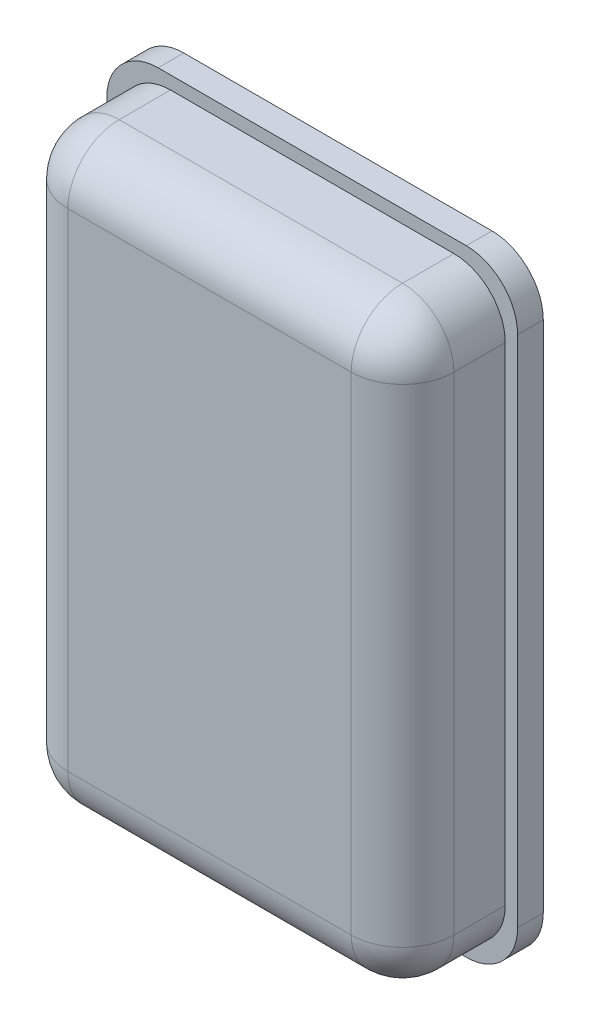
SolidWorks part; units mm, degrees
ref_plane "Alzado" through (0, 0, 0) normal (0, 0, 1) x (1, 0, 0)
ref_plane "Planta" through (0, 0, 0) normal (0, 1, 0) x (1, 0, 0)
ref_plane "Vista lateral" through (0, 0, 0) normal (1, 0, 0) x (0, 0, -1)
sketch "Croquis1" plane through (0, 0, 0) normal (0, 0, 1) x (1, 0, 0)
  line L1 (40, 60) -> (-40, 60)
  line L2 (40, 60) -> (40, -60)
  line L3 (40, -60) -> (-40, -60)
  line L4 (-40, 60) -> (-40, -60)
  line L5 (40, 60) -> (-40, -60) construction
  line L6 (40, -60) -> (-40, 60) construction
  point P0 (0, 0)
  dimension "D1" = 80
  dimension "D2" = 120
extrude "Saliente-Extruir1" add sketch "Croquis1" along normal blind 5
fillet "Redondeo2" radius 10 4 edges at (-40, -60, 2.5) (40, -60, 2.5) (-40, 60, 2.5) (40, 60, 2.5)
sketch "Croquis2" plane through (0, 0, 5) normal (0, 0, 1) x (1, 0, 0)
  line L1 (-37.5888, 57.4644) -> (37.5888, 57.4644)
  line L2 (-37.5888, 57.4644) -> (-37.5888, -57.4644)
  line L3 (-37.5888, -57.4644) -> (37.5888, -57.4644)
  line L4 (37.5888, 57.4644) -> (37.5888, -57.4644)
  line L5 (-37.5888, 57.4644) -> (37.5888, -57.4644) construction
  line L6 (-37.5888, -57.4644) -> (37.5888, 57.4644) construction
  point P0 (0, 0)
extrude "Saliente-Extruir2" add sketch "Croquis2" along normal blind 20 separate body
fillet "Redondeo1" radius 10 8 edges at (0, -57.4644, 25) (-37.5888, 0, 25) (0, 57.4644, 25) (37.5888, 0, 25) (-37.5888, 57.4644, 15) (-37.5888, -57.4644, 15) (37.5888, -57.4644, 15) (37.5888, 57.4644, 15)
